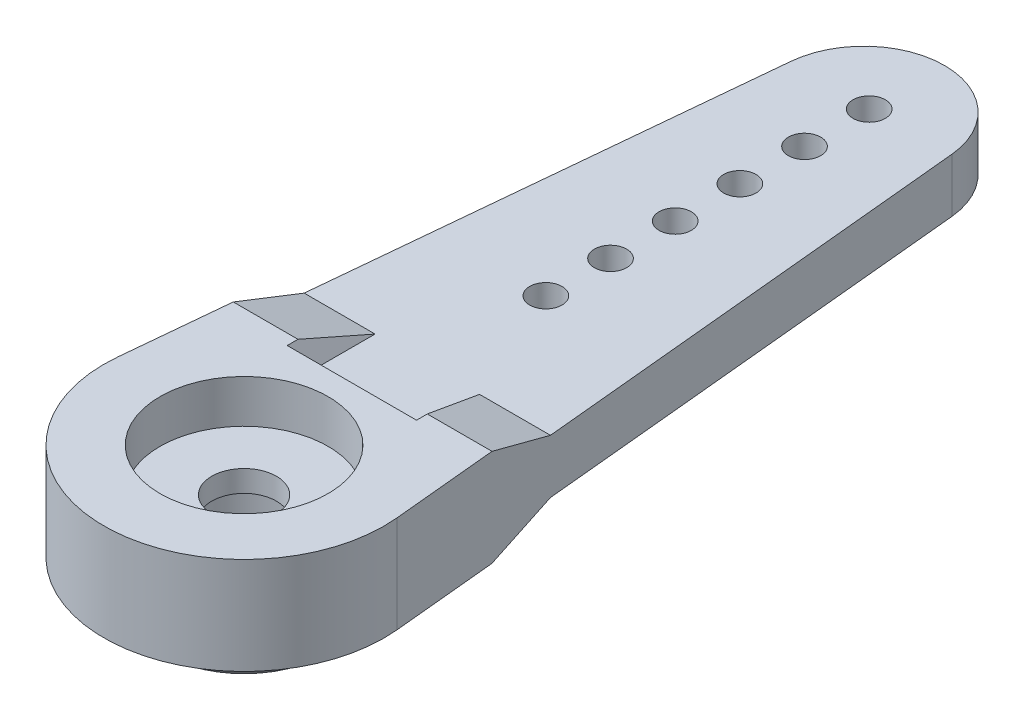
SolidWorks part; units mm, degrees
ref_plane "Front Plane" through (0, 0, 0) normal (0, 0, 1) x (1, 0, 0)
ref_plane "Top Plane" through (0, 0, 0) normal (0, 1, 0) x (1, 0, 0)
ref_plane "Right Plane" through (0, 0, 0) normal (1, 0, 0) x (0, 0, -1)
sketch "Sketch1" plane through (0, 0, 0) normal (0, 1, 0) x (1, 0, 0)
  line L0 (-6.4702, 0.6217) -> (-3.7328, 29.1087)
  line L1 (3.7328, 29.1087) -> (6.4702, 0.6217)
  line L2 (0, 29) -> (0, 26) construction
  line L3 (0, 26) -> (0, 23) construction
  line L4 (0, 23) -> (0, 20) construction
  line L5 (0, 20) -> (0, 17) construction
  line L6 (0, 17) -> (0, 14) construction
  arc A0 (-6.4702, 0.6217) -> (6.4702, 0.6217) centre (0, 0) ccw
  arc A1 (3.7328, 29.1087) -> (-3.7328, 29.1087) centre (0, 28.75) ccw
  circle A2 centre (0, 29) radius 0.75
  circle A3 centre (0, 26) radius 0.75
  circle A4 centre (0, 23) radius 0.75
  circle A5 centre (0, 20) radius 0.75
  circle A6 centre (0, 17) radius 0.75
  circle A7 centre (0, 14) radius 0.75
  dimension "D1" = 6.5
  dimension "D2" = 39
  dimension "D3" = 3.75
  dimension "D5" = 1.5
  dimension "D4" = 15
  dimension "D6" = 14
extrude "Boss-Extrude1" add sketch "Sketch1" along normal mid plane 4.5
sketch "Sketch2" plane through (0, 0, 0) normal (1, 0, 0) x (0, 0, -1)
  line L0 (5.5, 2.25) -> (32.5, 2.25)
  line L1 (32.5, 2.25) -> (32.5, 1.25)
  line L2 (32.5, 1.25) -> (8.5, 1.25)
  line L3 (8.5, 1.25) -> (5.5, 2.25)
  line L4 (0.6217, 2.25) -> (29.1087, 2.25) construction
  line L5 (32.5, -2.25) -> (32.5, 2.25) construction
  line L7 (-6.5, 2.25) -> (-6.5, -2.25) construction
  dimension "D1" = 1.25
  dimension "D2" = 12
  dimension "D3" = 3
extrude "Cut-Extrude1" cut sketch "Sketch2" against normal mid plane 14
sketch "Sketch3" plane through (0, 2.25, 0) normal (0, 1, 0) x (1, 0, 0)
  line L0 (0, 0) -> (0, 5) construction
  line L1 (-3, 5) -> (3, 5)
  line L2 (-3, 5) -> (-3, 8.5)
  line L3 (-3, 8.5) -> (3, 8.5)
  line L4 (3, 5) -> (3, 8.5)
  line L6 (-5.7132, 8.5) -> (5.7132, 8.5) construction
  arc A1 (-6.4702, 0.6217) -> (6.4702, 0.6217) centre (0, 0) ccw construction
  dimension "D1" = 11.5
  dimension "D2" = 6
extrude "Cut-Extrude2" cut sketch "Sketch3" against normal up to surface (1 mm away) up to face at (0, 1.25, -29.75)
mirror "Mirror1" about plane through (0, 0, 0) normal (0, 1, 0) of "Cut-Extrude1", "Cut-Extrude2"
draft "Draft1" type of draft neutral plane draft angle 30 faces to draft 3 face at (0, 1.75, -5) face at (-3, 1.75, -6) face at (3, 1.75, -6) neutral plane through (0, 2.25, 0) neutral plane normal (0, 1, 0) parameters "D1"=30
draft "Draft2" type of draft neutral plane draft angle 30 faces to draft 3 face at (-3, -1.75, -6) face at (0, -1.75, -5) face at (3, -1.75, -6) neutral plane through (0, -2.25, 0) neutral plane normal (0, -1, 0) parameters "D1"=30
sketch "Sketch4" plane through (0, 2.25, 0) normal (0, 1, 0) x (1, 0, 0)
  circle A0 centre (0, 0) radius 3.9
  dimension "D1" = 7.8
extrude "Cut-Extrude3" cut sketch "Sketch4" against normal blind 2
sketch "Sketch5" plane through (0, -2.25, 0) normal (0, -1, 0) x (1, 0, 0)
  circle A0 centre (0, 0) radius 4.8
  dimension "D1" = 9.6
extrude "Boss-Extrude2" add sketch "Sketch5" along normal blind 2 contours A0
chamfer "Chamfer1" distance 1 angle 45 1 edges at (0, -4.25, -4.8)
sketch "Sketch6" plane through (0, -4.25, 0) normal (0, -1, 0) x (1, 0, 0)
  circle A0 centre (0, 0) radius 3
  dimension "D1" = 6
extrude "Cut-Extrude4" cut sketch "Sketch6" against normal blind 3.5
sketch "Sketch7" plane through (0, -0.75, 0) normal (0, -1, 0) x (1, 0, 0)
  circle A0 centre (0, 0) radius 1.5
  dimension "D1" = 3
extrude "Cut-Extrude5" cut sketch "Sketch7" against normal through all
